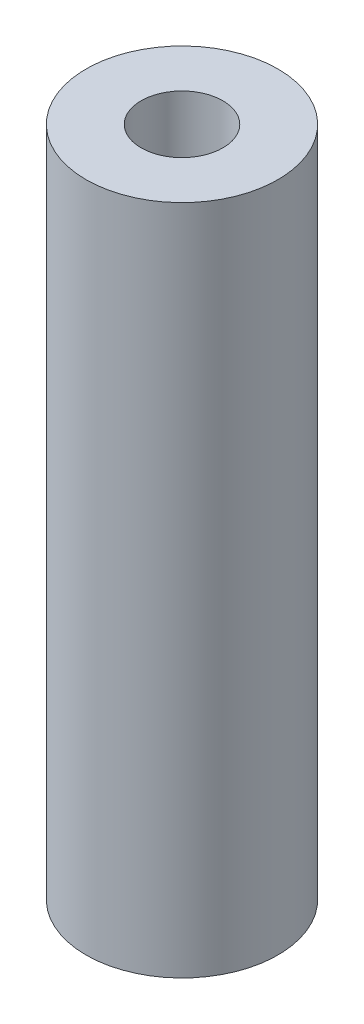
SolidWorks part; units mm, degrees
ref_plane "Front Plane" through (0, 0, 0) normal (0, 0, 1) x (1, 0, 0)
ref_plane "Top Plane" through (0, 0, 0) normal (0, 1, 0) x (1, 0, 0)
ref_plane "Right Plane" through (0, 0, 0) normal (1, 0, 0) x (0, 0, -1)
sketch "Sketch1" plane through (0, 0, 0) normal (0, 1, 0) x (1, 0, 0)
  circle A0 centre (0, 0) radius 3.175
  dimension "D1" = 6.35
extrude "Boss-Extrude1" add sketch "Sketch1" along normal blind 22.225
hole_wizard "Tap Drill for #6-32 Tap1" positions "Sketch3" profile "Sketch2" hole size "#6-32" standard "ANSI Inch" end condition through all
sketch "Sketch3" plane through (0, 22.225, 0) normal (0, 1, 0) x (1, 0, 0)
  point P0 (0, 0)
sketch "Sketch2" plane through (0, 22.225, 0) normal (1, 0, 0) x (0, 0, 1)
  line L0 (0, 0) -> (0, 22.225)
  line L1 (0, 22.225) -> (1.3525, 22.225)
  line L2 (1.3525, 22.225) -> (1.3525, 0)
  line L5 (1.3525, 0) -> (0, 0)
  line L11 (0, -6.35) -> (0, 107.95) construction
  dimension "Thru Hole Dia." = 2.7051
  dimension "Thru Hole Depth" = 22.225
